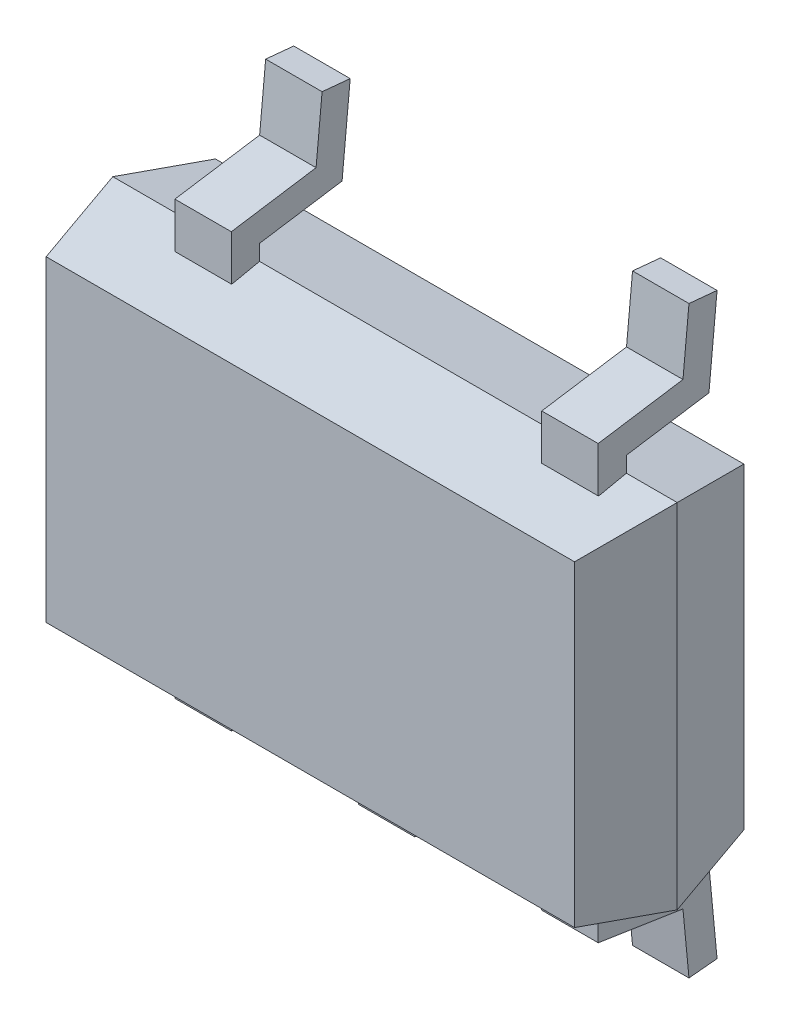
SolidWorks part; units mm, degrees
ref_plane "Front Plane" through (0, 0, 0) normal (0, 0, 1) x (1, 0, 0)
ref_plane "Top Plane" through (0, 0, 0) normal (0, 1, 0) x (1, 0, 0)
ref_plane "Right Plane" through (0, 0, 0) normal (1, 0, 0) x (0, 0, -1)
sketch "Sketch1" plane through (0, 0, 0) normal (0, 0, 1) x (1, 0, 0)
  line L1 (0, 0) -> (2, 0)
  line L2 (0, 0) -> (0, 1.25)
  line L3 (0, 1.25) -> (2, 1.25)
  line L4 (2, 0) -> (2, 1.25)
  dimension "D1" = 1.25
  dimension "D2" = 2
extrude "Boss-Extrude1" add sketch "Sketch1" along normal blind 0.3 draft 12
sketch "Sketch2" plane through (0, 0, 0) normal (0, 0, -1) x (-1, 0, 0)
  line L1 (-2, 1.25) -> (0, 1.25)
  line L2 (-2, 1.25) -> (-2, 0)
  line L3 (-2, 0) -> (0, 0)
  line L4 (0, 1.25) -> (0, 0)
extrude "Boss-Extrude2" add sketch "Sketch2" along normal blind 0.3 draft 12
ref_plane "Plane1" through (0.42, 0, 0) normal (1, 0, 0) x (0, 0, -1)
ref_plane "Plane2" through (0, 0.625, 0) normal (0, 1, 0) x (1, 0, 0)
sketch "Sketch3" plane through (0.42, 0, 0) normal (1, 0, 0) x (0, 0, -1)
  line L0 (0, 0.0196) -> (0, -0.0553)
  line L1 (0, -0.0553) -> (0.2925, -0.1004)
  line L2 (0.2925, -0.1004) -> (0.3212, -0.4004)
  line L3 (0, 1.25) -> (0, 0) construction
  point P2 (0.2928, -0.2219)
  point P3 (0.3, -0.1537)
  point P6 (0, 0)
  point P7 (0, 0)
  point P8 (0.2836, -0.2834)
  point P9 (0, 0)
  point P10 (0, 0)
  point P11 (0, 0)
  point P12 (0, 0)
  point P13 (0, 0)
  point P14 (0, 0)
  point P15 (0, 0)
  point P16 (0, 0)
  point P17 (0, 0)
  point P18 (0, 0.0296)
  point P19 (0.3, -0.2128)
  point P20 (0.3216, -0.6163)
  point P21 (0.3, -0.2179)
  point P22 (0, 0)
  point P23 (0, 0.0437)
  dimension "D1" = 0.3
  dimension "D2" = 0.42
extrude "Extrude-Thin1" add sketch "Sketch3" along normal mid plane 0.2 separate body thin
mirror "Mirror9" about plane through (0, 0.625, 0) normal (0, 1, 0) of "Extrude-Thin1"
pattern_linear "LPattern2" count 3 spacing 0.65 along (1, 0, 0) of "Extrude-Thin1"
pattern_linear "LPattern5" count 2 spacing 1.3 along (1, 0, 0) of "Mirror9", "Extrude-Thin1"
